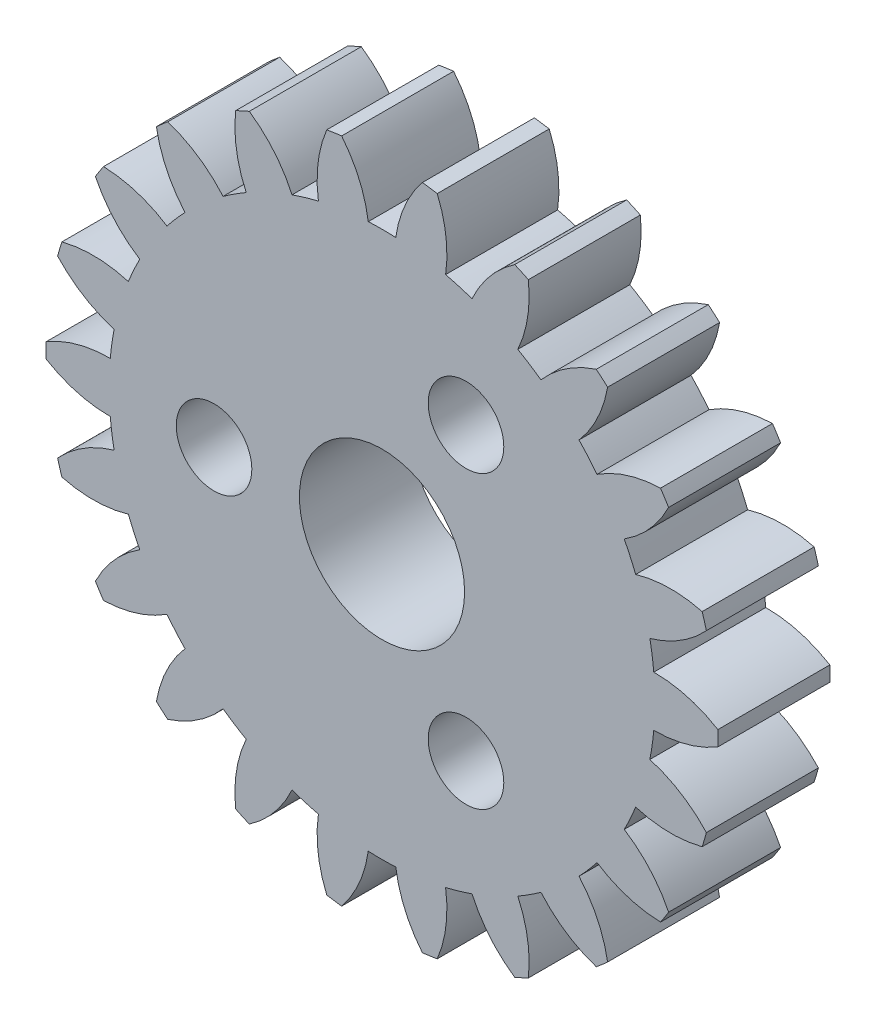
SolidWorks part; units mm, degrees
ref_plane "Front Plane" through (0, 0, 0) normal (0, 0, 1) x (1, 0, 0)
ref_plane "Top Plane" through (0, 0, 0) normal (0, 1, 0) x (1, 0, 0)
ref_plane "Right Plane" through (0, 0, 0) normal (1, 0, 0) x (0, 0, -1)
sketch "Model" plane through (0, 0, 0) normal (0, 0, 1) x (1, 0, 0)
  circle A0 centre (0, 0) radius 2.5
  arc A1 (-11.997, 0.2683) -> (-11.997, -0.2683) centre (0, 0) ccw
  arc A2 (-9.7074, 0.8997) -> (-11.997, 0.2683) centre (-9.7259, -3.5003) ccw
  arc A3 (-9.5676, 1.8717) -> (-9.7074, 0.8997) centre (0, 0) ccw
  arc A4 (-11.5866, 3.1225) -> (-9.5676, 1.8717) centre (-8.3458, 6.0986) ccw
  arc A5 (-11.4355, 3.6374) -> (-11.5866, 3.1225) centre (0, 0) ccw
  arc A6 (-9.0607, 3.5981) -> (-11.4355, 3.6374) centre (-10.3181, -0.6184) ccw
  arc A7 (-8.6528, 4.4914) -> (-9.0607, 3.5981) centre (0, 0) ccw
  arc A8 (-10.2376, 6.2604) -> (-8.6528, 4.4914) centre (-6.2896, 8.2029) ccw
  arc A9 (-9.9475, 6.7118) -> (-10.2376, 6.2604) centre (0, 0) ccw
  arc A10 (-7.68, 6.0051) -> (-9.9475, 6.7118) centre (-10.0744, 2.3136) ccw
  arc A11 (-7.0369, 6.7472) -> (-7.68, 6.0051) centre (0, 0) ccw
  arc A12 (-8.0591, 8.891) -> (-7.0369, 6.7472) centre (-3.7238, 9.6426) ccw
  arc A13 (-7.6536, 9.2424) -> (-8.0591, 8.891) centre (0, 0) ccw
  arc A14 (-5.6771, 7.9255) -> (-7.6536, 9.2424) centre (-9.0145, 5.0582) ccw
  arc A15 (-4.851, 8.4564) -> (-5.6771, 7.9255) centre (0, 0) ccw
  arc A16 (-5.2278, 10.8014) -> (-4.851, 8.4564) centre (-0.8563, 10.3011) ccw
  arc A17 (-4.7397, 11.0243) -> (-5.2278, 10.8014) centre (0, 0) ccw
  arc A18 (-3.2142, 9.2039) -> (-4.7397, 11.0243) centre (-7.2243, 7.3929) ccw
  arc A19 (-2.272, 9.4806) -> (-3.2142, 9.2039) centre (0, 0) ccw
  arc A20 (-1.9729, 11.8367) -> (-2.272, 9.4806) centre (2.0805, 10.1251) ccw
  arc A21 (-1.4418, 11.9131) -> (-1.9729, 11.8367) centre (0, 0) ccw
  arc A22 (-0.491, 9.7366) -> (-1.4418, 11.9131) centre (-4.8488, 9.1288) ccw
  arc A23 (0.491, 9.7366) -> (-0.491, 9.7366) centre (0, 0) ccw
  arc A24 (1.4418, 11.9131) -> (0.491, 9.7366) centre (4.8488, 9.1288) ccw
  arc A25 (1.9729, 11.8367) -> (1.4418, 11.9131) centre (0, 0) ccw
  arc A26 (2.272, 9.4806) -> (1.9729, 11.8367) centre (-2.0805, 10.1251) ccw
  arc A27 (3.2142, 9.2039) -> (2.272, 9.4806) centre (0, 0) ccw
  arc A28 (4.7397, 11.0243) -> (3.2142, 9.2039) centre (7.2243, 7.3929) ccw
  arc A29 (5.2278, 10.8014) -> (4.7397, 11.0243) centre (0, 0) ccw
  arc A30 (4.851, 8.4564) -> (5.2278, 10.8014) centre (0.8563, 10.3011) ccw
  arc A31 (5.6771, 7.9255) -> (4.851, 8.4564) centre (0, 0) ccw
  arc A32 (7.6536, 9.2424) -> (5.6771, 7.9255) centre (9.0145, 5.0582) ccw
  arc A33 (8.0591, 8.891) -> (7.6536, 9.2424) centre (0, 0) ccw
  arc A34 (7.0369, 6.7472) -> (8.0591, 8.891) centre (3.7238, 9.6426) ccw
  arc A35 (7.68, 6.0051) -> (7.0369, 6.7472) centre (0, 0) ccw
  arc A36 (9.9475, 6.7118) -> (7.68, 6.0051) centre (10.0744, 2.3136) ccw
  arc A37 (10.2376, 6.2604) -> (9.9475, 6.7118) centre (0, 0) ccw
  arc A38 (8.6528, 4.4914) -> (10.2376, 6.2604) centre (6.2896, 8.2029) ccw
  arc A39 (9.0607, 3.5981) -> (8.6528, 4.4914) centre (0, 0) ccw
  arc A40 (11.4355, 3.6374) -> (9.0607, 3.5981) centre (10.3181, -0.6184) ccw
  arc A41 (11.5866, 3.1225) -> (11.4355, 3.6374) centre (0, 0) ccw
  arc A42 (9.5676, 1.8717) -> (11.5866, 3.1225) centre (8.3458, 6.0986) ccw
  arc A43 (9.7074, 0.8997) -> (9.5676, 1.8717) centre (0, 0) ccw
  arc A44 (11.997, 0.2683) -> (9.7074, 0.8997) centre (9.7259, -3.5003) ccw
  arc A45 (11.997, -0.2683) -> (11.997, 0.2683) centre (0, 0) ccw
  arc A46 (9.7074, -0.8997) -> (11.997, -0.2683) centre (9.7259, 3.5003) ccw
  arc A47 (9.5676, -1.8717) -> (9.7074, -0.8997) centre (0, 0) ccw
  arc A48 (11.5866, -3.1225) -> (9.5676, -1.8717) centre (8.3458, -6.0986) ccw
  arc A49 (11.4355, -3.6374) -> (11.5866, -3.1225) centre (0, 0) ccw
  arc A50 (9.0607, -3.5981) -> (11.4355, -3.6374) centre (10.3181, 0.6184) ccw
  arc A51 (8.6528, -4.4914) -> (9.0607, -3.5981) centre (0, 0) ccw
  arc A52 (10.2376, -6.2604) -> (8.6528, -4.4914) centre (6.2896, -8.2029) ccw
  arc A53 (9.9475, -6.7118) -> (10.2376, -6.2604) centre (0, 0) ccw
  arc A54 (7.68, -6.0051) -> (9.9475, -6.7118) centre (10.0744, -2.3136) ccw
  arc A55 (7.0369, -6.7472) -> (7.68, -6.0051) centre (0, 0) ccw
  arc A56 (8.0591, -8.891) -> (7.0369, -6.7472) centre (3.7238, -9.6426) ccw
  arc A57 (7.6536, -9.2424) -> (8.0591, -8.891) centre (0, 0) ccw
  arc A58 (5.6771, -7.9255) -> (7.6536, -9.2424) centre (9.0145, -5.0582) ccw
  arc A59 (4.851, -8.4564) -> (5.6771, -7.9255) centre (0, 0) ccw
  arc A60 (5.2278, -10.8014) -> (4.851, -8.4564) centre (0.8563, -10.3011) ccw
  arc A61 (4.7397, -11.0243) -> (5.2278, -10.8014) centre (0, 0) ccw
  arc A62 (3.2142, -9.2039) -> (4.7397, -11.0243) centre (7.2243, -7.3929) ccw
  arc A63 (2.272, -9.4806) -> (3.2142, -9.2039) centre (0, 0) ccw
  arc A64 (1.9729, -11.8367) -> (2.272, -9.4806) centre (-2.0805, -10.1251) ccw
  arc A65 (1.4418, -11.9131) -> (1.9729, -11.8367) centre (0, 0) ccw
  arc A66 (0.491, -9.7366) -> (1.4418, -11.9131) centre (4.8488, -9.1288) ccw
  arc A67 (-0.491, -9.7366) -> (0.491, -9.7366) centre (0, 0) ccw
  arc A68 (-1.4418, -11.9131) -> (-0.491, -9.7366) centre (-4.8488, -9.1288) ccw
  arc A69 (-1.9729, -11.8367) -> (-1.4418, -11.9131) centre (0, 0) ccw
  arc A70 (-2.272, -9.4806) -> (-1.9729, -11.8367) centre (2.0805, -10.1251) ccw
  arc A71 (-3.2142, -9.2039) -> (-2.272, -9.4806) centre (0, 0) ccw
  arc A72 (-4.7397, -11.0243) -> (-3.2142, -9.2039) centre (-7.2243, -7.3929) ccw
  arc A73 (-5.2278, -10.8014) -> (-4.7397, -11.0243) centre (0, 0) ccw
  arc A74 (-4.851, -8.4564) -> (-5.2278, -10.8014) centre (-0.8563, -10.3011) ccw
  arc A75 (-5.6771, -7.9255) -> (-4.851, -8.4564) centre (0, 0) ccw
  arc A76 (-7.6536, -9.2424) -> (-5.6771, -7.9255) centre (-9.0145, -5.0582) ccw
  arc A77 (-8.0591, -8.891) -> (-7.6536, -9.2424) centre (0, 0) ccw
  arc A78 (-7.0369, -6.7472) -> (-8.0591, -8.891) centre (-3.7238, -9.6426) ccw
  arc A79 (-7.68, -6.0051) -> (-7.0369, -6.7472) centre (0, 0) ccw
  arc A80 (-9.9475, -6.7118) -> (-7.68, -6.0051) centre (-10.0744, -2.3136) ccw
  arc A81 (-10.2376, -6.2604) -> (-9.9475, -6.7118) centre (0, 0) ccw
  arc A82 (-8.6528, -4.4914) -> (-10.2376, -6.2604) centre (-6.2896, -8.2029) ccw
  arc A83 (-9.0607, -3.5981) -> (-8.6528, -4.4914) centre (0, 0) ccw
  arc A84 (-11.4355, -3.6374) -> (-9.0607, -3.5981) centre (-10.3181, 0.6184) ccw
  arc A85 (-11.5866, -3.1225) -> (-11.4355, -3.6374) centre (0, 0) ccw
  arc A86 (-9.5676, -1.8717) -> (-11.5866, -3.1225) centre (-8.3458, -6.0986) ccw
  arc A87 (-9.7074, -0.8997) -> (-9.5676, -1.8717) centre (0, 0) ccw
  arc A88 (-11.997, -0.2683) -> (-9.7074, -0.8997) centre (-9.7259, 3.5003) ccw
extrude "Boss-Extrude1" add sketch "Model" along normal blind 4
sketch "Sketch4" plane through (0, 0, 0) normal (0, 0, 1) x (1, 0, 0)
  circle A0 centre (0, 0) radius 11 construction
  dimension "D1" = 22
sketch "Sketch2" plane through (0, 0, 4) normal (0, 0, 1) x (1, 0, 0)
  circle A0 centre (0, 0) radius 2.95
  dimension "D1" = 5.9
extrude "Cut-Extrude1" cut sketch "Sketch2" against normal blind 4
sketch "Sketch3" plane through (0, 0, 4) normal (0, 0, 1) x (1, 0, 0)
  line L0 (0, 0) -> (-9.3925, 0) construction
  line L1 (0, 0) -> (-6, 0) construction
  circle A0 centre (-6, 0) radius 1.35
  dimension "D1" = 2.7
  dimension "D2" = 6
  dimension "D3" = 0
extrude "Cut-Extrude2" cut sketch "Sketch3" against normal blind 4
pattern_circular "CirPattern1" count 3 over 360 about axis through (0, 0, 0) along (0, 0, 1) of "Cut-Extrude2"
